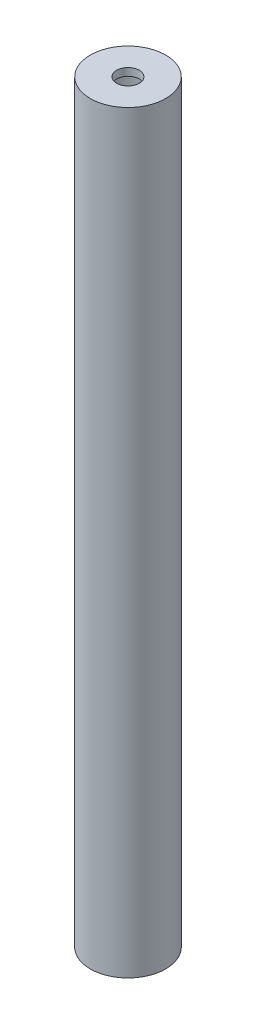
SolidWorks part; units mm, degrees
material "Gray Cast Iron"
ref_plane "Front Plane" through (0, 0, 0) normal (0, 0, 1) x (1, 0, 0)
ref_plane "Top Plane" through (0, 0, 0) normal (0, 1, 0) x (1, 0, 0)
ref_plane "Right Plane" through (0, 0, 0) normal (1, 0, 0) x (0, 0, -1)
sketch "Sketch1" plane through (0, 0, 0) normal (0, 1, 0) x (1, 0, 0)
  circle A0 centre (0, 0) radius 10
  dimension "D1" = 20
extrude "Boss-Extrude1" add sketch "Sketch1" along normal blind 200
shell "Shell1" thickness 2
sketch "Sketch2" plane through (0, 200, 0) normal (0, 1, 0) x (1, 0, 0)
  circle A0 centre (0, 0) radius 3
  dimension "D1" = 6
extrude "Cut-Extrude1" cut sketch "Sketch2" against normal through all both
